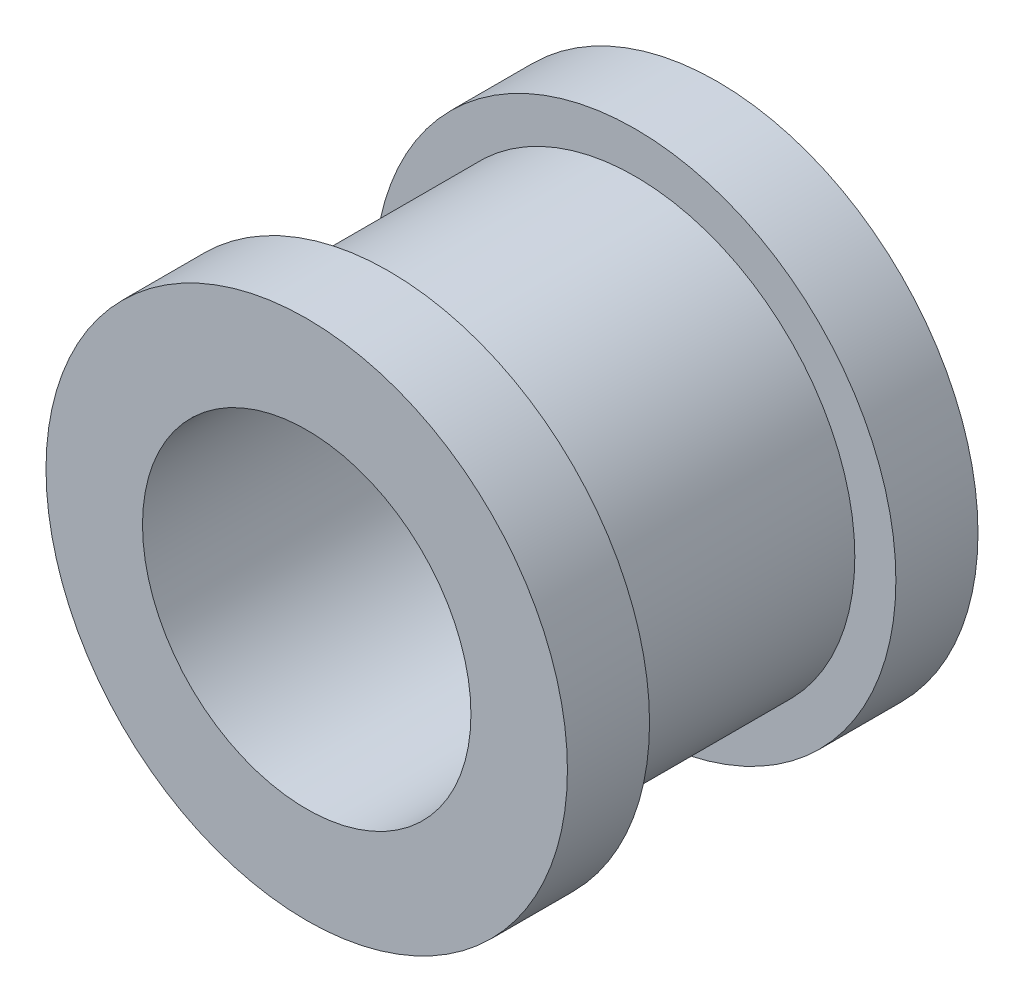
SolidWorks part; units mm, degrees
ref_plane "Alzado" through (0, 0, 0) normal (0, 0, 1) x (1, 0, 0)
ref_plane "Planta" through (0, 0, 0) normal (0, 1, 0) x (1, 0, 0)
ref_plane "Vista lateral" through (0, 0, 0) normal (1, 0, 0) x (0, 0, -1)
sketch "Croquis1" plane through (0, 0, 0) normal (0, 0, 1) x (1, 0, 0)
  circle A0 centre (0, 0) radius 6.35
  circle A1 centre (0, 0) radius 4
  dimension "D1" = 12.7
  dimension "D2" = 8
extrude "Saliente-Extruir1" add sketch "Croquis1" along normal blind 10
sketch "Croquis2" plane through (0, 0, 0) normal (1, 0, 0) x (0, 0, -1)
  line L0 (0, 6.35) -> (-10, 6.35) construction
  line L1 (-2, 6.35) -> (-8, 6.35)
  line L2 (-2, 6.35) -> (-2, 5.35)
  line L3 (-2, 5.35) -> (-8, 5.35)
  line L4 (-8, 6.35) -> (-8, 5.35)
  line L5 (0, -6.35) -> (0, 6.35) construction
  line L6 (-10, 6.35) -> (-10, -6.35) construction
  dimension "D1" = 2
  dimension "D2" = 2
  dimension "D3" = 1
ref_axis "Eje1" through (0, 0, 10) along (0, 0, -1)
revolve "Cortar-Revolución1" cut sketch "Croquis2" angle 360 about axis through (0, 0, 10) along (0, 0, -1)
